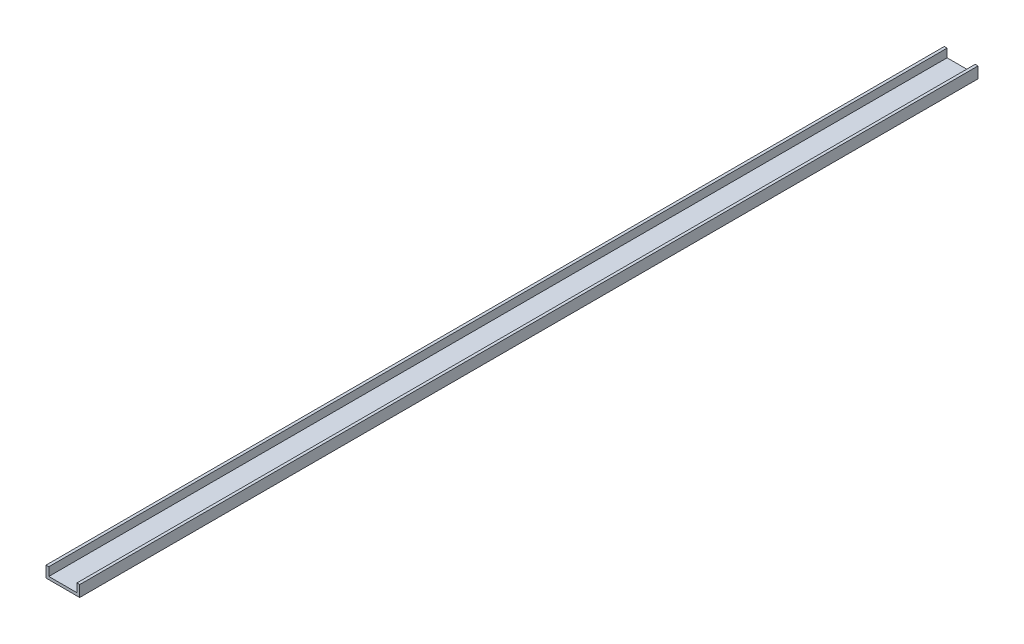
SolidWorks part; units mm, degrees
ref_plane "Front" through (0, 0, 0) normal (0, 0, 1) x (1, 0, 0)
ref_plane "Top" through (0, 0, 0) normal (0, 1, 0) x (1, 0, 0)
ref_plane "Right" through (0, 0, 0) normal (1, 0, 0) x (0, 0, -1)
sketch "Sketch1" plane through (0, 0, 0) normal (0, 0, 1) x (1, 0, 0)
  line L0 (3.175, 3.175) -> (3.175, 12.7)
  line L1 (0, 0) -> (38.1, 0)
  line L2 (0, 0) -> (0, 12.7)
  line L4 (38.1, 0) -> (38.1, 12.7)
  line L5 (3.175, 3.175) -> (34.925, 3.175)
  line L6 (34.925, 3.175) -> (34.925, 12.7)
  line L7 (0, 12.7) -> (3.175, 12.7)
  line L8 (38.1, 12.7) -> (34.925, 12.7)
  dimension "D1" = 12.7
  dimension "D2" = 38.1
  dimension "D3" = 3.175
extrude "f" add sketch "Sketch1" along normal blind 1016
